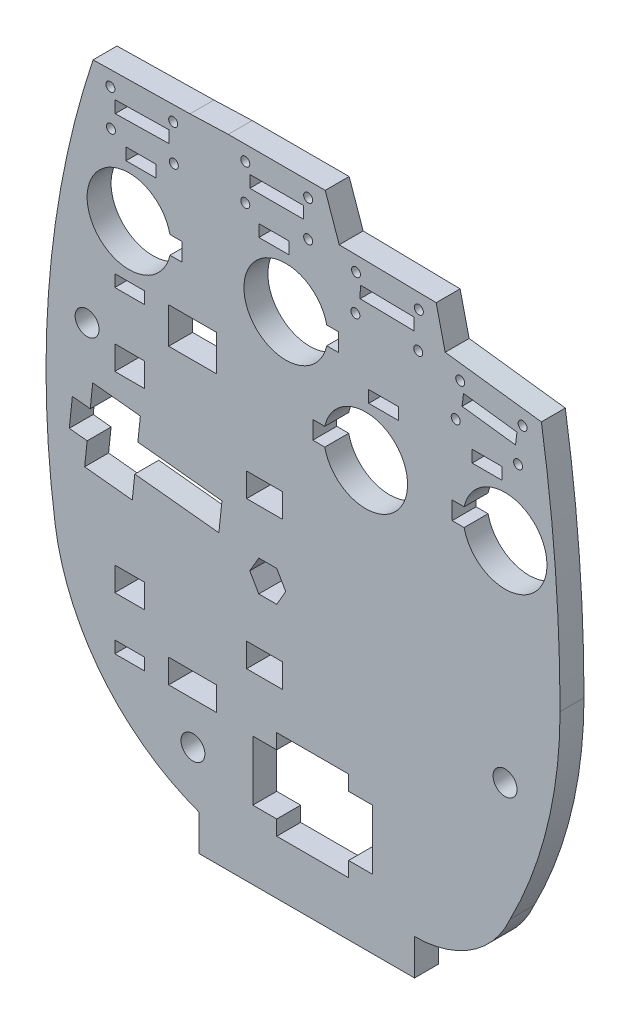
SolidWorks part; units mm, degrees
ref_plane "Front Plane" through (0, 0, 0) normal (0, 0, 1) x (1, 0, 0)
ref_plane "Top Plane" through (0, 0, 0) normal (0, 1, 0) x (1, 0, 0)
ref_plane "Right Plane" through (0, 0, 0) normal (1, 0, 0) x (0, 0, -1)
sketch "Sketch1" plane through (0, 0, 0) normal (0, 0, 1) x (1, 0, 0)
  line L0 (-4.5, 78.51) -> (-4.5, 76.51)
  line L1 (4.5, 78.51) -> (-4.5, 78.51)
  line L2 (-12.9786, -18) -> (-12.9786, -24)
  line L3 (-9.666, 24.0723) -> (-9.153, 28.9531)
  line L4 (-4.5, 76.51) -> (4.5, 76.51)
  line L5 (4.5, 76.51) -> (4.5, 78.51)
  line L6 (-34.6568, 26.6989) -> (-34.1438, 31.5798)
  line L7 (10.3588, 63.1512) -> (10.3588, 60.1512)
  line L8 (-8.1, 82.51) -> (8.1, 82.51)
  line L9 (8.3588, 63.1512) -> (10.3588, 63.1512)
  line L10 (10.4412, 75.8064) -> (26.6388, 75.5236)
  line L11 (32.6473, 57.3216) -> (37.6473, 57.3216)
  line L12 (0, 0) -> (-22.59, 0) construction
  line L13 (10.3588, 60.1512) -> (8.3588, 60.1512)
  line L14 (-17.8416, 63.1512) -> (-15.8416, 63.1512)
  line L15 (-15.8416, 63.1512) -> (-15.8416, 60.1512)
  line L16 (-15.8416, 60.1512) -> (-17.8416, 60.1512)
  line L17 (32.6473, 55.3216) -> (37.6473, 55.3216)
  line L18 (37.6473, 55.3216) -> (37.6473, 57.3216)
  line L19 (32.6473, 57.3216) -> (32.6473, 55.3216)
  line L20 (-27.0195, 78.062) -> (-18.0208, 78.2192)
  line L21 (-27.0195, 78.062) -> (-26.9845, 76.0623)
  line L22 (-10.0543, 52.8756) -> (-18.0543, 52.8756)
  line L23 (-9.153, 28.9531) -> (-23.2041, 30.43)
  line L24 (-26.9845, 76.0623) -> (-17.9858, 76.2195)
  line L25 (-24.1352, 21.571) -> (-32.0914, 22.4072)
  line L26 (-32.0914, 22.4072) -> (-31.6733, 26.3853)
  line L27 (-23.7171, 25.5491) -> (-9.666, 24.0723)
  line L28 (-17.9858, 76.2195) -> (-18.0208, 78.2192)
  line L29 (15.3631, 57.3216) -> (20.3631, 57.3216)
  line L30 (15.3631, 55.3216) -> (20.3631, 55.3216)
  line L31 (-12.9786, -24) -> (23.0214, -24)
  line L32 (20.3631, 55.3216) -> (20.3631, 57.3216)
  line L33 (23.0214, -24) -> (23.0214, -18)
  line L34 (15.3631, 57.3216) -> (15.3631, 55.3216)
  line L35 (-2.9786, 72.1512) -> (2.0214, 72.1512)
  line L36 (13.9709, 71.7441) -> (13.936, 69.7444)
  line L37 (13.936, 69.7444) -> (22.9346, 69.5874)
  line L38 (8.0257, 48.3216) -> (6.0257, 48.3216)
  line L39 (-2.9786, 70.1512) -> (2.0214, 70.1512)
  line L40 (22.9695, 71.5871) -> (13.9709, 71.7441)
  line L41 (6.0257, 48.3216) -> (6.0257, 45.3216)
  line L42 (22.9346, 69.5874) -> (22.9695, 71.5871)
  line L43 (-22.59, 0) -> (-22.59, 82.14) construction
  line L44 (2.0214, 70.1512) -> (2.0214, 72.1512)
  line L45 (18.54, 75.665) -> (18.5934, 78.7251) construction
  line L46 (-2.9786, 72.1512) -> (-2.9786, 70.1512)
  line L47 (40.1436, 63.5476) -> (31.2139, 64.6755)
  line L48 (6.0257, 45.3216) -> (8.0257, 45.3216)
  line L49 (29.3099, 45.3216) -> (31.3099, 45.3216)
  line L50 (29.3099, 48.3216) -> (29.3099, 45.3216)
  line L51 (31.3099, 48.3216) -> (29.3099, 48.3216)
  line L52 (-22.786, 34.408) -> (-30.7422, 35.2443)
  line L53 (31.2139, 64.6755) -> (30.9632, 62.6912)
  line L54 (-25.179, 72.1512) -> (-20.179, 72.1512)
  line L55 (-30.6888, 81.9985) -> (-14.4912, 82.2815)
  line L56 (44.2162, 67.065) -> (28.1438, 69.095)
  line L57 (-25.179, 70.1512) -> (-20.179, 70.1512)
  line L58 (30.9632, 62.6912) -> (39.893, 61.5633)
  line L59 (-20.179, 70.1512) -> (-20.179, 72.1512)
  line L60 (-25.179, 72.1512) -> (-25.179, 70.1512)
  line L61 (39.893, 61.5633) -> (40.1436, 63.5476)
  line L62 (-34.6568, 26.6989) -> (-31.6733, 26.3853)
  line L63 (-4, -2.5) -> (0, -2.5)
  line L64 (12, 0) -> (0, 0)
  line L65 (12, 0) -> (12, -2.5)
  line L66 (12, -15) -> (0, -15)
  line L67 (-30.7422, 35.2443) -> (-31.1603, 31.2662)
  line L68 (-23.2041, 30.43) -> (-22.786, 34.408)
  line L69 (-34.1438, 31.5798) -> (-31.1603, 31.2662)
  line L70 (-24.1352, 21.571) -> (-23.7171, 25.5491)
  line L71 (16, -7.5) -> (38.9913, -7.5) construction
  line L72 (0, -15) -> (0, -12.5)
  line L73 (-4, -12.5) -> (-4, -2.5)
  line L74 (-4, -12.5) -> (0, -12.5)
  line L75 (0, -2.5) -> (0, 0)
  line L76 (0, 0) -> (0, 82.51) construction
  line L77 (-22.0543, 52.8756) -> (-27.0543, 52.8756)
  line L78 (-10.0543, -2.1244) -> (-18.0543, -2.1244)
  line L79 (-22.0543, -2.1244) -> (-27.0543, -2.1244)
  line L80 (0, 0) -> (18.54, 0) construction
  line L81 (16, -12.5) -> (12, -12.5)
  line L82 (16, -12.5) -> (16, -2.5)
  line L83 (16, -2.5) -> (12, -2.5)
  line L84 (12, -12.5) -> (12, -15)
  line L85 (-9.4095, 26.5127) -> (6.8682, 24.8018) construction
  line L86 (0, 23.7547) -> (-3, 23.7547)
  line L87 (-3, 23.7547) -> (-4.5, 21.1566)
  line L88 (-4.5, 21.1566) -> (-3, 18.5585)
  line L89 (18.54, 0) -> (18.54, 75.665) construction
  line L90 (0, 0) -> (36.18, 0) construction
  line L91 (36.18, 0) -> (36.18, 68.08) construction
  line L92 (28.1438, 69.095) -> (26.6388, 75.5236)
  line L93 (10.4412, 75.8064) -> (8.1, 82.51)
  line L94 (-8.1, 82.51) -> (-14.4912, 82.2815)
  line L95 (-34.6568, 26.6989) -> (47.3354, 26.6989) construction
  line L96 (35.6788, 64.1115) -> (36.18, 68.08) construction
  line L97 (-3, 18.5585) -> (0, 18.5585)
  line L98 (0, 18.5585) -> (1.5, 21.1566)
  line L99 (1.5, 21.1566) -> (0, 23.7547)
  line L100 (0, 18.5585) -> (-3, 23.7547) construction
  line L101 (0, 23.7547) -> (-3, 18.5585) construction
  line L102 (38.1473, 11.8216) -> (-37.0527, 11.8216) construction
  line L103 (-27.7956, 79.5486) -> (-30.6451, 79.4989) construction
  line L104 (0.9634, 10.717) -> (0.9634, 6.717)
  line L105 (0.9634, 6.717) -> (-5.0366, 6.717)
  line L106 (-5.0366, 6.717) -> (-5.0366, 10.717)
  line L107 (-5.0366, 10.717) -> (0.9634, 10.717)
  line L108 (-5.0366, 31.3356) -> (0.9634, 31.3356)
  line L109 (-5.0366, 35.3356) -> (-5.0366, 31.3356)
  line L110 (0.9634, 35.3356) -> (-5.0366, 35.3356)
  line L111 (0.9634, 31.3356) -> (0.9634, 35.3356)
  line L112 (-30.6451, 79.4989) -> (-30.6888, 81.9985) construction
  line L113 (-17.2971, 79.732) -> (-14.4475, 79.7819) construction
  line L114 (-14.4475, 79.7819) -> (-14.4912, 82.2815) construction
  line L115 (-22.5201, 78.1406) -> (-22.59, 82.14) construction
  line L116 (5.25, 80.01) -> (8.1, 80.01) construction
  line L117 (8.1, 80.01) -> (8.1, 82.51) construction
  line L118 (-5.25, 80.01) -> (-8.1, 80.01) construction
  line L119 (-22.0543, -0.1244) -> (-27.0543, -0.1244)
  line L120 (-8.1, 80.01) -> (-8.1, 82.51) construction
  line L121 (-10.0543, 1.8756) -> (-10.0543, -2.1244)
  line L122 (30.6581, 66.2576) -> (27.8306, 66.6147) construction
  line L123 (-10.0543, 52.8756) -> (-10.0543, 46.8756)
  line L124 (-10.0543, 1.8756) -> (-18.0543, 1.8756)
  line L125 (-18.0543, 1.8756) -> (-18.0543, -2.1244)
  line L126 (27.8306, 66.6147) -> (28.1438, 69.095) construction
  line L127 (13.2472, 73.257) -> (10.3976, 73.3067) construction
  line L128 (-22.0543, -0.1244) -> (-22.0543, -2.1244)
  line L129 (-27.0543, -0.1244) -> (-27.0543, -2.1244)
  line L130 (30.6581, 66.2576) -> (29.9062, 60.3049) construction
  line L131 (-10.0543, 46.8756) -> (-18.0543, 46.8756)
  line L132 (-27.0543, 52.8756) -> (-27.0543, 50.8756)
  line L133 (-18.0543, 46.8756) -> (-18.0543, 52.8756)
  line L134 (10.4412, 75.8064) -> (10.3976, 73.3067) construction
  line L135 (-22.0543, 6.717) -> (-22.0543, 10.717)
  line L136 (-22.0543, 10.717) -> (-27.0543, 10.717)
  line L137 (-27.0543, 50.8756) -> (-22.0543, 50.8756)
  line L138 (-22.0543, 52.8756) -> (-22.0543, 50.8756)
  line L139 (-27.0543, 10.717) -> (-27.0543, 6.717)
  line L140 (-27.0543, 6.717) -> (-22.0543, 6.717)
  line L141 (-27.0543, 38.7272) -> (-22.0543, 38.7272)
  line L142 (-22.0543, 38.7272) -> (-22.0543, 42.7272)
  line L143 (-22.0543, 42.7272) -> (-27.0543, 42.7272)
  line L144 (-27.0543, 42.7272) -> (-27.0543, 38.7272)
  line L145 (23.7456, 73.0738) -> (26.5951, 73.024) construction
  line L146 (26.5951, 73.024) -> (26.6388, 75.5236) construction
  line L147 (41.0753, 64.9418) -> (43.9029, 64.5847) construction
  line L148 (41.0753, 64.9418) -> (40.3235, 58.9891) construction
  line L149 (40.3235, 58.9891) -> (43.151, 58.632) construction
  line L150 (43.151, 58.632) -> (43.9029, 64.5847) construction
  line L151 (23.7456, 73.0738) -> (23.6409, 67.0747) construction
  line L152 (13.2472, 73.257) -> (13.1425, 67.2579) construction
  line L153 (-17.2971, 79.732) -> (-17.1923, 73.733) construction
  line L154 (-27.7956, 79.5486) -> (-27.6908, 73.5496) construction
  line L155 (38.1473, 46.8216) -> (38.1473, 11.8216) construction
  arc A0 (-37.0527, 11.8216) -> (-30.6888, 81.9985) centre (116.3395, 33.2885) cw
  circle A1 centre (-1.5, 21.1566) radius 4.5 construction
  arc A2 (8.3588, 63.1512) -> (8.3588, 60.1512) centre (1.5214, 61.6512) ccw
  arc A3 (8.0257, 45.3216) -> (8.0257, 48.3216) centre (14.8631, 46.8216) ccw
  arc A4 (-17.8416, 63.1512) -> (-17.8416, 60.1512) centre (-24.679, 61.6512) ccw
  arc A5 (31.3099, 45.3216) -> (31.3099, 48.3216) centre (38.1473, 46.8216) ccw
  arc A6 (23.0214, -18) -> (38.9913, -7.5) centre (23.0214, -0.6053) ccw
  arc A7 (47.3354, 26.6989) -> (38.9913, -7.5) centre (-26.9196, 26.6989) cw
  arc A8 (-37.0527, 11.8216) -> (-12.9786, -18) centre (-0.147, 16.9865) ccw
  arc A9 (47.3354, 26.6989) -> (44.2162, 67.065) centre (-215.4084, 26.6989) ccw
  circle A11 centre (38.1473, 11.8216) radius 2
  circle A12 centre (-14, -9.1244) radius 2
  circle A18 centre (-5.25, 80.01) radius 0.75
  circle A22 centre (-31.6815, 43.4564) radius 2
  circle A49 centre (5.25, 80.01) radius 0.75
  circle A50 centre (5.25, 74.01) radius 0.75
  circle A51 centre (-5.25, 74.01) radius 0.75
  circle A52 centre (-27.7956, 79.5486) radius 0.75
  circle A53 centre (-17.2971, 79.732) radius 0.75
  circle A54 centre (-27.6908, 73.5496) radius 0.75
  circle A55 centre (-17.1923, 73.733) radius 0.75
  circle A56 centre (23.6409, 67.0747) radius 0.75
  circle A57 centre (13.1425, 67.2579) radius 0.75
  circle A58 centre (23.7456, 73.0738) radius 0.75
  circle A59 centre (13.2472, 73.257) radius 0.75
  circle A60 centre (29.9062, 60.3049) radius 0.7496
  circle A61 centre (41.0753, 64.9418) radius 0.7496
  circle A62 centre (30.6581, 66.2576) radius 0.7496
  circle A63 centre (40.3235, 58.9891) radius 0.7496
  dimension "D1" = 4
  dimension "D2" = 1.5
  dimension "D5" = 7
  dimension "D45" = 9
  dimension "D10" = 0.9634
  dimension "D11" = 1.5214
  dimension "D12" = 2.0214
  dimension "D16" = 6.0257
  dimension "D18" = 8.3588
  dimension "D26" = 15.3631
  dimension "D30" = 20.3631
  dimension "D33" = 23.0214
  dimension "D38" = 29.3099
  dimension "D42" = 32.6473
  dimension "D49" = 5.0366
  dimension "D50" = 9.153
  dimension "D51" = 9.666
  dimension "D52" = 10.0543
  dimension "D53" = 12.9786
  dimension "D54" = 14
  dimension "D56" = 15.8416
  dimension "D59" = 18.0543
  dimension "D62" = 20.179
  dimension "D63" = 22.0543
  dimension "D68" = 31.6815
  dimension "D71" = 1.8756
  dimension "D72" = 6.717
  dimension "D76" = 21.571
  dimension "D77" = 31.3356
  dimension "D79" = 43.4564
  dimension "D80" = 45.3216
  dimension "D81" = 46.8756
  dimension "D82" = 55.3216
  dimension "D84" = 60.1512
  dimension "D86" = 70.1512
  dimension "D93" = 9.1244
  dimension "D14" = 82.51
  dimension "D19" = 22.59
  dimension "D21" = 82.14
  dimension "D22" = 4
  dimension "D23" = 18.54
  dimension "D24" = 75.665
  dimension "D31" = 36.18
  dimension "D32" = 68.08
  dimension "D35" = 4
  dimension "D36" = 16.2
  dimension "D37" = 2
  dimension "D40" = 46.8216
  dimension "D41" = 14.8631
  dimension "D44" = 24.679
  dimension "D15" = 3
  dimension "D28" = 0
  dimension "D46" = 0.7292
  dimension "D47" = 4.9078
  dimension "D48" = 25.1285
  dimension "D55" = 24
  dimension "D20" = 10
  dimension "D25" = 12
  dimension "D27" = 2.5
  dimension "D57" = 4
  dimension "D66" = 2.85
  dimension "D67" = 2.5
  dimension "D78" = 6
  dimension "D13" = 4
  dimension "D43" = 2.85
  dimension "D58" = 2.5
  dimension "D64" = 2.5
  dimension "D65" = 2.85
  dimension "D39" = 2.85
  dimension "D70" = 2.5
  dimension "D17" = 4
  dimension "D73" = 9.0001
  dimension "D74" = 9.0007
  dimension "D29" = 2.5
  dimension "D34" = 6
  dimension "D61" = 6
  dimension "D60" = 8.1
  dimension "D69" = 6
  dimension "D83" = 8.1
  dimension "D75" = 35
  dimension "D85" = 2
extrude "Boss-Extrude1" add sketch "Sketch1" along normal blind 4
equation "\"D14@Sketch1\"= \"HL@parametersSketch@prostheticParameters.SLDPRT\" * 0.446'Mioddle Base Frame "
equation "\"D19@Sketch1\"= \"HB@parametersSketch@prostheticParameters.SLDPRT\" * 0.251'Index Base Frame X"
equation "\"D21@Sketch1\"= \"HL@parametersSketch@prostheticParameters.SLDPRT\" * 0.444'Index Base Frame Y"
equation "\"D23@Sketch1\"= \"HB@parametersSketch@prostheticParameters.SLDPRT\" * 0.206'Ring Base Frame X"
equation "\"D24@Sketch1\"= \"HL@parametersSketch@prostheticParameters.SLDPRT\" * 0.409'Ring Base Frame Y"
equation "\"D31@Sketch1\"= \"HB@parametersSketch@prostheticParameters.SLDPRT\" * 0.402'Pinky Base Frame X"
equation "\"D32@Sketch1\"= \"HL@parametersSketch@prostheticParameters.SLDPRT\" * 0.368'Pinky Base Frame Y"
equation "\"D36@Sketch1\"= \"fingerWidth@parametersSketch@prostheticParameters.SLDPRT\"'Fingers Width"
equation "\"D76@Sketch1\"= \"HL@parametersSketch@prostheticParameters.SLDPRT\" * 0.1166'Hole Thumb Y"
equation "\"D51@Sketch1\"= \"HB@parametersSketch@prostheticParameters.SLDPRT\" * 0.1074'Hole Thumb X1"
equation "\"D50@Sketch1\" = \"HB@parametersSketch@prostheticParameters.SLDPRT\" * 0.1017'Hole Thumb X2"
equation "\"D73@Sketch1\"= \"fingerWidth@parametersSketch@prostheticParameters.SLDPRT\" * 0.55556"
equation "\"D74@Sketch1\"= \"fingerWidth@parametersSketch@prostheticParameters.SLDPRT\" * 0.5556"
equation "\"D60@Sketch1\"= \"fingerWidth@parametersSketch@prostheticParameters.SLDPRT\" / 2"
equation "\"D83@Sketch1\"= \"fingerWidth@parametersSketch@prostheticParameters.SLDPRT\" / 2"
